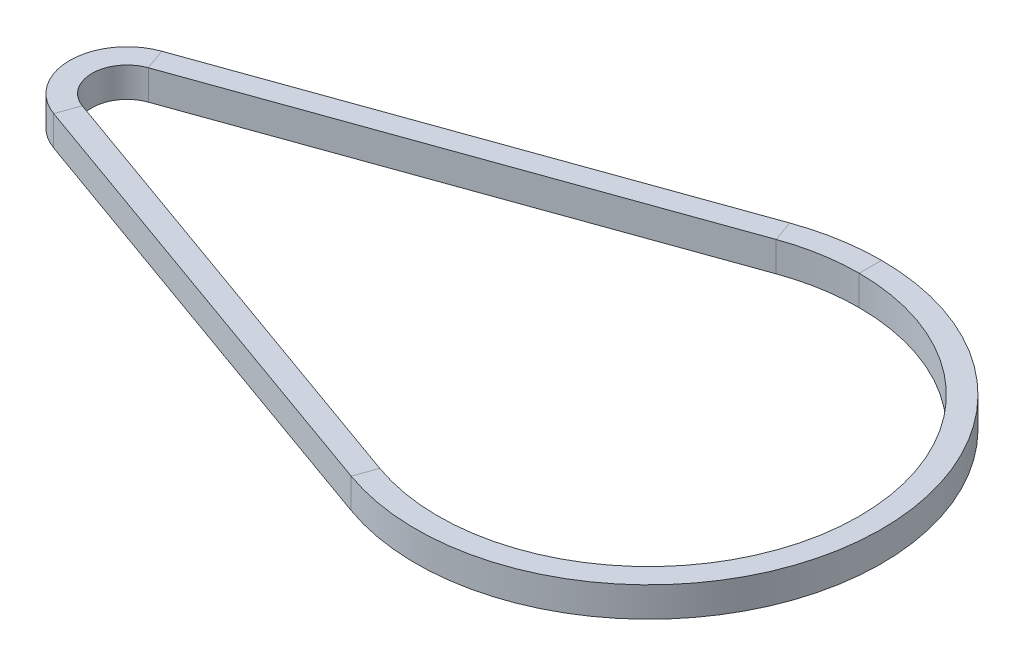
SolidWorks part; units mm, degrees
ref_plane "Front Plane" through (0, 0, 0) normal (0, 0, 1) x (1, 0, 0)
ref_plane "Top Plane" through (0, 0, 0) normal (0, 1, 0) x (1, 0, 0)
ref_plane "Right Plane" through (0, 0, 0) normal (1, 0, 0) x (0, 0, -1)
sketch "Sketch1" plane through (0, 0, 0) normal (0, 1, 0) x (1, 0, 0)
  line L0 (0, 0) -> (115.3838, 0) construction
  line L1 (115.3838, 0) -> (-96.6527, 0) construction
  line L2 (-1.5805, 4.4263) -> (60.5033, 26.5953)
  line L3 (-1.5805, -4.4263) -> (60.5033, -26.5953)
  arc A0 (-1.5805, 4.4263) -> (-1.5805, -4.4263) centre (0, 0) ccw
  arc A1 (60.5033, -26.5953) -> (60.5033, 26.5953) centre (70, 0) ccw construction
  arc A2 (60.5033, -26.5953) -> (60.5033, 26.5953) centre (70, 0) ccw
  arc A3 (60.5033, -26.5953) -> (60.1428, 26.4638) centre (70, 0) ccw construction
  dimension "D1" = 56.48
  dimension "D3" = 9.4
  dimension "D2" = 70
ref_plane "Plane1" through (70, 0, 0) normal (1, 0, 0) x (0, 0, -1)
sketch "Sketch2" plane through (70, 0, 0) normal (1, 0, 0) x (0, 0, -1)
  line L0 (28.24, 0) -> (-28.24, 0) construction
  line L1 (44.8101, 0) -> (-28.24, 0) construction
  line L3 (31.24, -2) -> (28.24, -2)
  line L4 (31.24, -2) -> (31.24, 2)
  line L5 (31.24, 2) -> (28.24, 2)
  line L6 (28.24, -2) -> (28.24, 2)
  dimension "D1" = 28.24
  dimension "D2" = 3
  dimension "D3" = 4
sweep "Sweep1" add profiles "Sketch2" path "Sketch1"
